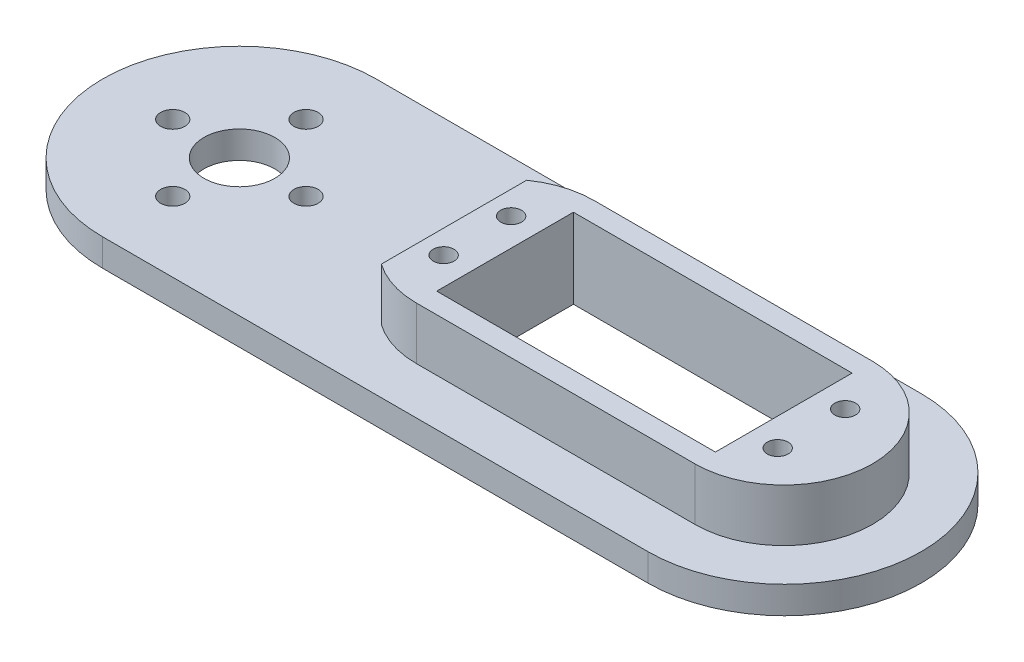
SolidWorks part; units mm, degrees
ref_plane "Front Plane" through (0, 0, 0) normal (0, 0, 1) x (1, 0, 0)
ref_plane "Top Plane" through (0, 0, 0) normal (0, 1, 0) x (1, 0, 0)
ref_plane "Right Plane" through (0, 0, 0) normal (1, 0, 0) x (0, 0, -1)
sketch "Sketch1" plane through (0, 0, 0) normal (0, 1, 0) x (1, 0, 0)
  line L0 (0, 15.5) -> (0, -15.5) construction
  line L1 (-15.5, 0) -> (15.5, 0) construction
  line L2 (-2.4674, 13.4022) -> (-4, 4) construction
  line L3 (4, -4) -> (-4, -4) construction
  line L4 (4, -4) -> (4, 4) construction
  line L5 (4, 4) -> (-4, 4) construction
  line L6 (-4, -4) -> (-4, 4) construction
  line L7 (4, -4) -> (-4, 4) construction
  line L8 (4, 4) -> (-4, -4) construction
  line L9 (-4, 4) -> (-2.4674, 13.4022)
  line L10 (4, 4) -> (2.4674, 13.4022)
  line L11 (4, -4) -> (2.4674, -13.4022)
  line L12 (-4, -4) -> (-2.4674, -13.4022)
  line L13 (-4, 4) -> (-12.5927, 2.4331) construction
  line L14 (-4, 4) -> (-12.4485, 2.4594)
  line L15 (-4, -4) -> (-12.4485, -2.4594)
  line L16 (4, -4) -> (12.4485, -2.4594)
  line L17 (4, 4) -> (12.4485, 2.4594)
  circle A0 centre (0, 0) radius 15.5 construction
  circle A1 centre (0, 0) radius 14.5 construction
  arc A2 (2.4674, 13.4022) -> (-2.4674, 13.4022) centre (0, 13) ccw
  arc A3 (2.4674, -13.4022) -> (-2.4674, -13.4022) centre (0, -13) cw
  arc A4 (-12.4485, 2.4594) -> (-12.4485, -2.4594) centre (-12, 0) ccw
  arc A5 (12.4485, 2.4594) -> (12.4485, -2.4594) centre (12, 0) cw
  circle A6 centre (0, 0) radius 12 construction
  circle A7 centre (0, 0) radius 9.5 construction
  circle A8 centre (0, 0) radius 7.5 construction
  circle A9 centre (0, 12) radius 0.5
  circle A10 centre (0, 9.5) radius 0.5
  circle A11 centre (0, 7.5) radius 0.5
  circle A12 centre (12, 0) radius 0.5
  circle A13 centre (9.5, 0) radius 0.5
  circle A14 centre (7.5, 0) radius 0.5
  circle A15 centre (0, -12) radius 0.5
  circle A16 centre (0, -9.5) radius 0.5
  circle A17 centre (0, -7.5) radius 0.5
  circle A18 centre (-12, 0) radius 0.5
  circle A19 centre (-9.5, 0) radius 0.5
  circle A20 centre (-7.5, 0) radius 0.5
  circle A21 centre (0, 0) radius 1.375
  point P59 (0, 0)
  dimension "D1" = 31
  dimension "D2" = 1
  dimension "D3" = 5
  dimension "D4" = 5
  dimension "D5" = 8
  dimension "D6" = 8
  dimension "D7" = 15
  dimension "D9" = 24
  dimension "D11" = 1
  dimension "D12" = 1
  dimension "D13" = 4
  dimension "D8" = 19
  dimension "D10" = 1
  dimension "D14" = 2.75
extrude "Boss-Extrude1" add sketch "Sketch1" along normal blind 2
sketch "Sketch4" plane through (0, 0, 0) normal (0, -1, 0) x (1, 0, 0)
  circle A0 centre (0, 0) radius 4.627
  circle A1 centre (0, 0) radius 2.627
  dimension "D1" = 9.254
  dimension "D2" = 2
extrude "Boss-Extrude3" add sketch "Sketch4" along normal blind 2.5
sketch "Sketch5" plane through (0, -2.5, 0) normal (0, -1, 0) x (1, 0, 0)
  line L0 (0, 0) -> (0, 0.6245) construction
  line L1 (0, 3.1016) -> (-0.2828, 2.6117)
  line L2 (0, 3.1016) -> (0.2828, 2.6117)
  line L3 (0.9584, 2.9498) -> (0.5381, 2.5713)
  line L4 (0.9584, 2.9498) -> (1.076, 2.3965)
  line L5 (1.8231, 2.5092) -> (1.3063, 2.2792)
  line L6 (1.8231, 2.5092) -> (1.7639, 1.9467)
  line L7 (2.5092, 1.8231) -> (1.9467, 1.7639)
  line L8 (2.5092, 1.8231) -> (2.2792, 1.3063)
  line L9 (2.9498, 0.9584) -> (2.3965, 1.076)
  line L10 (2.9498, 0.9584) -> (2.5713, 0.5381)
  line L11 (3.1016, 0) -> (2.6117, 0.2828)
  line L12 (3.1016, 0) -> (2.6117, -0.2828)
  line L13 (2.9498, -0.9584) -> (2.5713, -0.5381)
  line L14 (2.9498, -0.9584) -> (2.3965, -1.076)
  line L15 (2.5092, -1.8231) -> (2.2792, -1.3063)
  line L16 (2.5092, -1.8231) -> (1.9467, -1.7639)
  line L17 (1.8231, -2.5092) -> (1.7639, -1.9467)
  line L18 (1.8231, -2.5092) -> (1.3063, -2.2792)
  line L19 (0.9584, -2.9498) -> (1.076, -2.3965)
  line L20 (0.9584, -2.9498) -> (0.5381, -2.5713)
  line L21 (0, -3.1016) -> (0.2828, -2.6117)
  line L22 (0, -3.1016) -> (-0.2828, -2.6117)
  line L23 (-0.9584, -2.9498) -> (-0.5381, -2.5713)
  line L24 (-0.9584, -2.9498) -> (-1.076, -2.3965)
  line L25 (-1.8231, -2.5092) -> (-1.3063, -2.2792)
  line L26 (-1.8231, -2.5092) -> (-1.7639, -1.9467)
  line L27 (-2.5092, -1.8231) -> (-1.9467, -1.7639)
  line L28 (-2.5092, -1.8231) -> (-2.2792, -1.3063)
  line L29 (-2.9498, -0.9584) -> (-2.3965, -1.076)
  line L30 (-2.9498, -0.9584) -> (-2.5713, -0.5381)
  line L31 (-3.1016, 0) -> (-2.6117, -0.2828)
  line L32 (-3.1016, 0) -> (-2.6117, 0.2828)
  line L33 (-2.9498, 0.9584) -> (-2.5713, 0.5381)
  line L34 (-2.9498, 0.9584) -> (-2.3965, 1.076)
  line L35 (-2.5092, 1.8231) -> (-2.2792, 1.3063)
  line L36 (-2.5092, 1.8231) -> (-1.9467, 1.7639)
  line L37 (-1.8231, 2.5092) -> (-1.7639, 1.9467)
  line L38 (-1.8231, 2.5092) -> (-1.3063, 2.2792)
  line L39 (-0.9584, 2.9498) -> (-1.076, 2.3965)
  line L40 (-0.9584, 2.9498) -> (-0.5381, 2.5713)
  circle A0 centre (0, 0) radius 2.627 construction
  arc A1 (-2.2792, 1.3063) -> (-2.3965, 1.076) centre (0, 0) ccw
  arc A2 (-1.7639, 1.9467) -> (-1.9467, 1.7639) centre (0, 0) ccw
  arc A3 (-1.076, 2.3965) -> (-1.3063, 2.2792) centre (0, 0) ccw
  arc A4 (-0.2828, 2.6117) -> (-0.5381, 2.5713) centre (0, 0) ccw
  arc A5 (0.5381, 2.5713) -> (0.2828, 2.6117) centre (0, 0) ccw
  arc A6 (1.3063, 2.2792) -> (1.076, 2.3965) centre (0, 0) ccw
  arc A7 (1.9467, 1.7639) -> (1.7639, 1.9467) centre (0, 0) ccw
  arc A8 (2.3965, 1.076) -> (2.2792, 1.3063) centre (0, 0) ccw
  arc A9 (2.6117, 0.2828) -> (2.5713, 0.5381) centre (0, 0) ccw
  arc A10 (2.5713, -0.5381) -> (2.6117, -0.2828) centre (0, 0) ccw
  arc A11 (2.2792, -1.3063) -> (2.3965, -1.076) centre (0, 0) ccw
  arc A12 (1.7639, -1.9467) -> (1.9467, -1.7639) centre (0, 0) ccw
  arc A13 (1.076, -2.3965) -> (1.3063, -2.2792) centre (0, 0) ccw
  arc A14 (0.2828, -2.6117) -> (0.5381, -2.5713) centre (0, 0) ccw
  arc A15 (-0.5381, -2.5713) -> (0, -2.627) centre (0, 0) ccw
  arc A16 (-1.3063, -2.2792) -> (-1.076, -2.3965) centre (0, 0) ccw
  arc A17 (-1.9467, -1.7639) -> (-1.7639, -1.9467) centre (0, 0) ccw
  arc A18 (-2.3965, -1.076) -> (-2.2792, -1.3063) centre (0, 0) ccw
  arc A19 (-2.6117, -0.2828) -> (-2.5713, -0.5381) centre (0, 0) ccw
  arc A20 (-2.5713, 0.5381) -> (-2.6117, 0.2828) centre (0, 0) ccw
  point P68 (0, 0)
  circle M5 centre (0, 0) radius 2.627
  dimension "D1" = 30
  dimension "D2" = 3.1016
  dimension "D3" = 20
extrude "Cut-Extrude3" cut sketch "Sketch5" against normal up to surface (2.5 mm away) contours L36 L35 M5 | L34 L33 M5 | L32 L31 M5 | L30 L29 M5 | L28 L27 M5 | L26 L25 M5 | L24 L23 M5 | L0 L21 M5 | L22 L0 M5 | L20 L19 M5 | L18 L17 M5 | L16 L15 M5 | L14 L13 M5 | L12 L11 M5 | L10 L9 M5 | L8 L7 M5 | L6 L5 M5 | L4 L3 M5 | L0 L2 M5 | L0 L1 M5 | L40 L39 M5 | L38 L37 M5
sketch "Sketch6" plane through (0, 2, 0) normal (0, 1, 0) x (1, 0, 0)
  circle A0 centre (0, 0) radius 20.066
  circle A2 centre (0, 0) radius 3.75
  dimension "D1" = 40.132
extrude "Boss-Extrude6" add sketch "Sketch6" against normal blind 2.54
sketch "Sketch7" plane through (0, 2, 0) normal (0, 1, 0) x (1, 0, 0)
  circle A0 centre (0, 9.779) radius 1.778
extrude "Cut-Extrude4" cut sketch "Sketch7" against normal blind 2.54
pattern_circular "CirPattern1" count 4 over 360 about axis through (0, 0, 0) along (0, 1, 0) of "Cut-Extrude4"
sketch "Esquisse1" plane through (0, 2, 0) normal (0, 1, 0) x (1, 0, 0)
  line L0 (0, 20.066) -> (80.01, 20.066)
  line L1 (0, -20.066) -> (80.01, -20.066)
  circle A0 centre (0, 0) radius 20.066 construction
  arc A1 (80.01, 20.066) -> (80.01, -20.066) centre (80.01, 0) cw
  arc A2 (0, -20.066) -> (0, 20.066) centre (0, 0) ccw
  dimension "D1" = 80.01
  dimension "D2" = 80.01
extrude "Boss.-Extru.1" add sketch "Esquisse1" along normal blind 2.2225 and the other way blind 2.54 contours L1 A1 L0 A2
sketch "Esquisse3" plane through (0, 2, 0) normal (0, 1, 0) x (1, 0, 0)
  circle A0 centre (0, 0) radius 20.066
  circle A1 centre (9.779, 0) radius 1.778
  circle A2 centre (0, 9.779) radius 1.778
  circle A3 centre (-9.779, 0) radius 1.778
  circle A4 centre (0, -9.779) radius 1.778
  circle A5 centre (0, 0) radius 1.375
extrude "Boss.-Extru.2" add sketch "Esquisse3" along normal blind 2.2225
sketch "Esquisse4" plane through (0, -0.54, 0) normal (0, -1, 0) x (1, 0, 0)
  line L0 (0, 20.066) -> (80.01, 20.066) construction
  line L1 (80.01, 10.16) -> (39.116, 10.16)
  line L2 (39.116, 10.16) -> (39.116, -9.906)
  line L3 (39.116, -9.906) -> (80.01, -9.906)
  line L4 (80.01, -9.906) -> (80.01, 10.16)
  dimension "D1" = 9.906
  dimension "D2" = 20.066
  dimension "D3" = 40.894
extrude "Enlèv. mat.-Extru.1" cut sketch "Esquisse4" against normal up to next
sketch "Esquisse5" plane through (0, -0.54, 0) normal (0, -1, 0) x (-1, 0, 0)
  line L0 (-39.116, -10.16) -> (-39.116, 9.906) construction
  line L1 (-39.116, 9.906) -> (-80.01, 9.906) construction
  line L2 (-80.01, -10.16) -> (-39.116, -10.16) construction
  line L3 (-80.01, 9.906) -> (-80.01, -10.16) construction
  circle A0 centre (-35.052, -5.08) radius 1.524
  circle A1 centre (-35.052, 4.826) radius 1.524
  circle A2 centre (-84.074, -5.08) radius 1.524
  circle A3 centre (-84.074, 4.826) radius 1.524
  dimension "D2" = 4.064
  dimension "D3" = 5.08
  dimension "D4" = 5.08
  dimension "D5" = 5.08
  dimension "D6" = 5.08
  dimension "D7" = 4.064
  dimension "D8" = 4.064
  dimension "D9" = 3.048
  dimension "D10" = 3.048
  dimension "D11" = 3.048
  dimension "D12" = 3.048
  dimension "D1" = 4.064
extrude "Enlèv. mat.-Extru.2" cut sketch "Esquisse5" against normal through all
sketch "Esquisse6" plane through (0, 4.2225, 0) normal (0, 1, 0) x (1, 0, 0)
  line L1 (-24.0414, -40.1247) -> (105.7665, -40.1247)
  line L2 (-24.0414, -40.1247) -> (-24.0414, 44.3818)
  line L3 (-24.0414, 44.3818) -> (105.7665, 44.3818)
  line L4 (105.7665, -40.1247) -> (105.7665, 44.3818)
extrude "Enlèv. mat.-Extru.3" cut sketch "Esquisse6" against normal blind 0.76
sketch "Esquisse7" plane through (0, -2.5, 0) normal (0, -1, 0) x (-1, 0, 0)
  circle A0 centre (0, 0) radius 5.2
  dimension "D1" = 10.4
extrude "Enlèv. mat.-Extru.4" cut sketch "Esquisse7" against normal through all
sketch "Esquisse8" plane through (0, 3.4625, 0) normal (0, 1, 0) x (1, 0, 0)
  line L0 (80.01, -13.16) -> (39.116, -13.16)
  line L1 (80.01, 12.906) -> (39.116, 12.906)
  line L3 (39.116, -10.16) -> (80.01, -10.16)
  line L4 (39.116, -10.16) -> (39.116, 9.906)
  line L5 (39.116, 9.906) -> (80.01, 9.906)
  line L6 (80.01, -10.16) -> (80.01, 9.906)
  arc A0 (80.01, -13.16) -> (80.01, 12.906) centre (80.01, -0.127) ccw
  arc A1 (39.116, -13.16) -> (39.116, 12.906) centre (39.116, -0.127) cw
  circle A2 centre (84.074, -5.08) radius 1.524
  circle A3 centre (84.074, 4.826) radius 1.524
  circle A4 centre (35.052, -5.08) radius 1.524
  circle A5 centre (35.052, 4.826) radius 1.524
  dimension "D3" = 13.033
  dimension "D1" = 3
  dimension "D2" = 3
extrude "Boss.-Extru.3" add sketch "Esquisse8" along normal blind 7.7
sketch "Esquisse9" plane through (0, 11.1625, 0) normal (0, 1, 0) x (1, 0, 0)
  line L0 (31.616, 12.906) -> (24.1634, 12.906)
  line L1 (31.616, -13.16) -> (31.616, 12.906)
  line L2 (24.1634, 12.906) -> (24.1634, -13.16)
  line L3 (24.1634, -13.16) -> (31.616, -13.16)
extrude "Enlèv. mat.-Extru.5" cut sketch "Esquisse9" against normal blind 7.7
